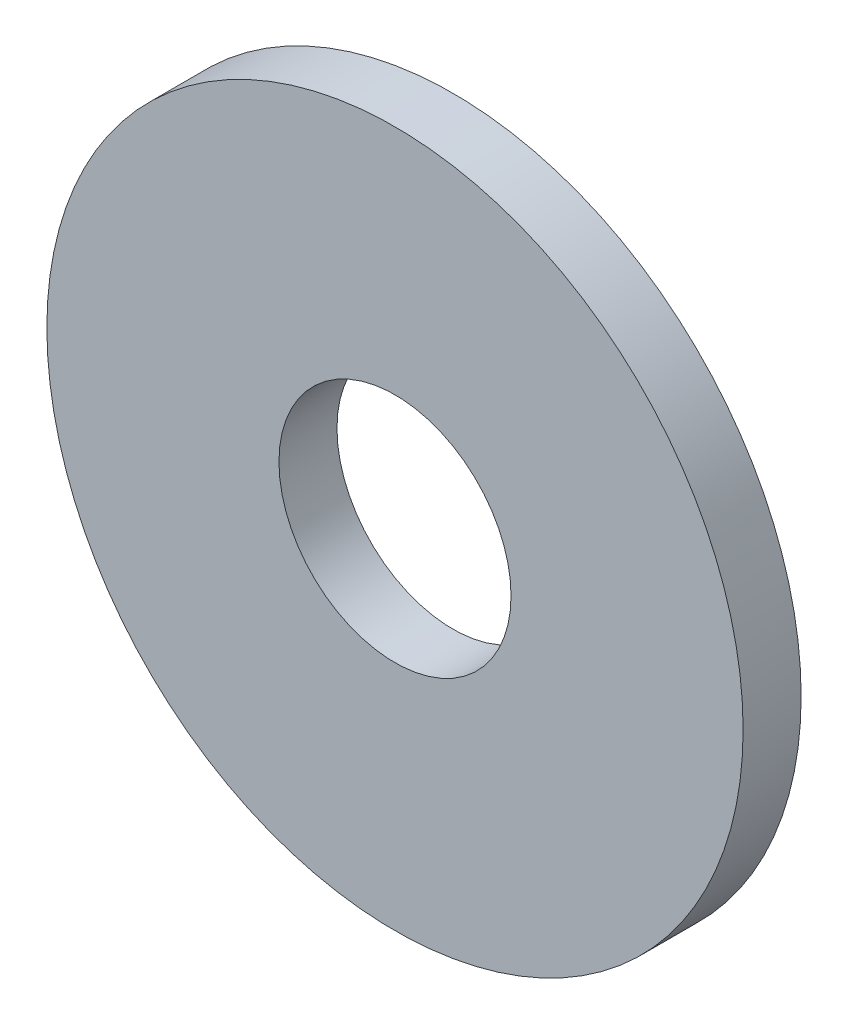
SolidWorks part; units mm, degrees
material "AISI 1020"
ref_plane "Front Plane" through (0, 0, 0) normal (0, 0, 1) x (1, 0, 0)
ref_plane "Top Plane" through (0, 0, 0) normal (0, 1, 0) x (1, 0, 0)
ref_plane "Right Plane" through (0, 0, 0) normal (1, 0, 0) x (0, 0, -1)
sketch "Sketch1" plane through (0, 0, 0) normal (0, 0, 1) x (1, 0, 0)
  circle A0 centre (0, 0) radius 3.175
  circle A1 centre (0, 0) radius 9.525
  dimension "D1" = 6.35
  dimension "D2" = 19.05
extrude "Boss-Extrude1" add sketch "Sketch1" along normal blind 1.5875
